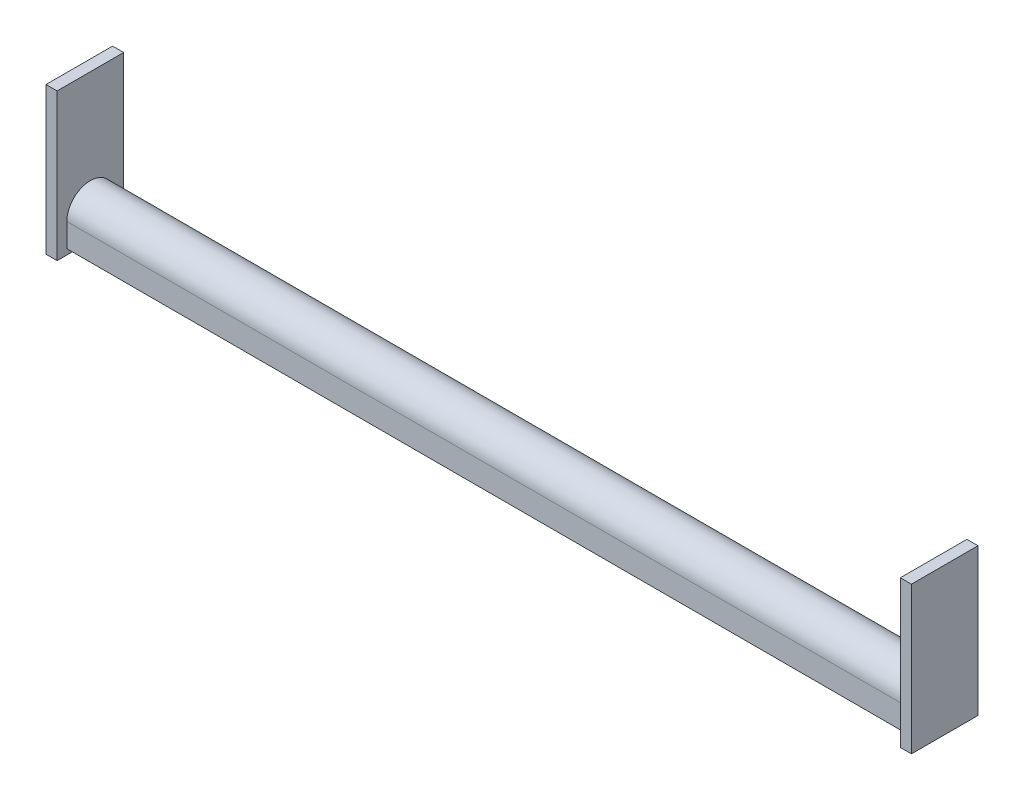
SolidWorks part; units mm, degrees
ref_plane "Front Plane" through (0, 0, 0) normal (0, 0, 1) x (1, 0, 0)
ref_plane "Top Plane" through (0, 0, 0) normal (0, 1, 0) x (1, 0, 0)
ref_plane "Right Plane" through (0, 0, 0) normal (1, 0, 0) x (0, 0, -1)
sketch "Sketch1" plane through (0, 0, 0) normal (1, 0, 0) x (0, 0, -1)
  line L1 (-38.1, 84.1375) -> (38.1, 84.1375)
  line L2 (-38.1, 84.1375) -> (-38.1, -84.1375)
  line L3 (-38.1, -84.1375) -> (38.1, -84.1375)
  line L4 (38.1, 84.1375) -> (38.1, -84.1375)
  line L5 (-38.1, 84.1375) -> (38.1, -84.1375) construction
  line L6 (-38.1, -84.1375) -> (38.1, 84.1375) construction
  point P0 (0, 0)
  dimension "D1" = 168.275
  dimension "D2" = 76.2
extrude "Boss-Extrude1" add sketch "Sketch1" along normal blind 12.7
sketch "Sketch2" plane through (0, 0, 0) normal (-1, 0, 0) x (0, 0, 1)
  line L0 (-26.9875, -77.7875) -> (-26.9875, -50.8)
  line L1 (-26.9875, -77.7875) -> (-22.9235, -77.7875)
  line L2 (-22.9235, -77.7875) -> (-22.9235, -50.8)
  line L3 (22.9235, -50.8) -> (22.9235, -77.7875)
  line L4 (22.9235, -77.7875) -> (26.9875, -77.7875)
  line L5 (26.9875, -77.7875) -> (26.9875, -50.8)
  line L6 (-22.9235, -50.8) -> (22.9235, -50.8) construction
  line L7 (-22.9235, -77.7875) -> (22.9235, -77.7875) construction
  line L8 (0, -50.8) -> (0, 0) construction
  line L9 (-26.9875, -50.8) -> (-22.9235, -50.8) construction
  line L10 (22.9235, -50.8) -> (26.9875, -50.8) construction
  line L11 (38.1, -84.1375) -> (-38.1, -84.1375) construction
  arc A0 (-22.9235, -50.8) -> (22.9235, -50.8) centre (0, -50.8) cw
  arc A1 (-26.9875, -50.8) -> (26.9875, -50.8) centre (0, -50.8) cw
  dimension "D3" = 26.9875
  dimension "D1" = 4.064
  dimension "D2" = 53.975
  dimension "D4" = 6.35
extrude "Boss-Extrude2" add sketch "Sketch2" along normal blind 965.2
sketch "Sketch3" plane through (-965.2, 0, 0) normal (-1, 0, 0) x (0, 0, 1)
  line L4 (-38.1, 84.1375) -> (-38.1, -84.1375)
  line L5 (-38.1, -84.1375) -> (38.1, -84.1375)
  line L6 (38.1, -84.1375) -> (38.1, 84.1375)
  line L7 (38.1, 84.1375) -> (-38.1, 84.1375)
  line L8 (-38.1, 84.1375) -> (-38.1, -84.1375)
  line L9 (-38.1, -84.1375) -> (38.1, -84.1375)
  line L10 (38.1, -84.1375) -> (38.1, 84.1375)
  line L11 (38.1, 84.1375) -> (-38.1, 84.1375)
  dimension "D1" = 0
extrude "Boss-Extrude3" add sketch "Sketch3" along normal blind 12.7
sketch "Sketch4" plane through (12.7, 0, 0) normal (1, 0, 0) x (0, 0, -1)
  line L0 (0, 46.0375) -> (0, 0) construction
  line L1 (38.1, 84.1375) -> (-38.1, 84.1375) construction
  circle A0 centre (0, 46.0375) radius 38.1 construction
  dimension "D1" = 76.2
  dimension "D2" = 38.1
sketch "Sketch5" plane through (-977.9, 0, 0) normal (-1, 0, 0) x (0, 0, 1)
  circle A0 centre (0, 46.0375) radius 38.1 construction
  circle A1 centre (0, 46.0375) radius 38.1 construction
